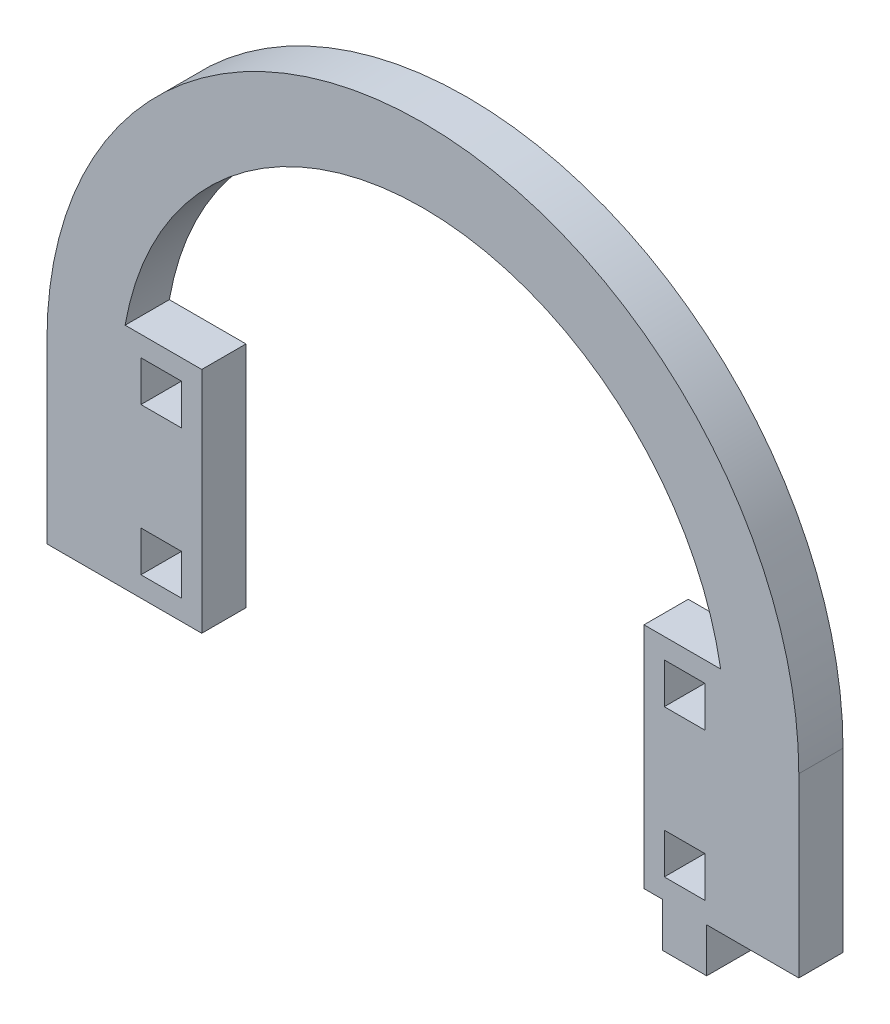
SolidWorks part; units mm, degrees
ref_plane "Front Plane" through (0, 0, 0) normal (0, 0, 1) x (1, 0, 0)
ref_plane "Top Plane" through (0, 0, 0) normal (0, 1, 0) x (1, 0, 0)
ref_plane "Right Plane" through (0, 0, 0) normal (1, 0, 0) x (0, 0, -1)
sketch "Model" plane through (0, 0, 0) normal (0, 0, 1) x (1, 0, 0)
  line L0 (3452.9004, 1295.0685) -> (3452.9004, 1271.0685)
  line L1 (3554.9004, 1295.0685) -> (3554.9004, 1271.0685)
  line L2 (3452.9004, 1271.0685) -> (3462.9004, 1271.0685)
  line L4 (3542.1504, 1279.3185) -> (3536.6504, 1279.3185)
  line L5 (3536.6504, 1279.3185) -> (3536.6504, 1273.8185)
  line L6 (3536.6504, 1273.8185) -> (3542.1504, 1273.8185)
  line L7 (3542.1504, 1273.8185) -> (3542.1504, 1279.3185)
  line L8 (3533.9004, 1271.0685) -> (3536.4004, 1271.0685)
  line L9 (3536.4004, 1271.0685) -> (3536.4004, 1265.0685)
  line L10 (3536.4004, 1265.0685) -> (3542.4004, 1265.0685)
  line L11 (3542.4004, 1265.0685) -> (3542.4004, 1271.0685)
  line L12 (3542.1504, 1299.3185) -> (3536.6504, 1299.3185)
  line L13 (3536.6504, 1299.3185) -> (3536.6504, 1293.8185)
  line L14 (3536.6504, 1293.8185) -> (3542.1504, 1293.8185)
  line L15 (3542.1504, 1293.8185) -> (3542.1504, 1299.3185)
  line L16 (3544.2984, 1302.0685) -> (3533.9004, 1302.0685)
  line L17 (3471.1504, 1279.3185) -> (3465.6504, 1279.3185)
  line L18 (3465.6504, 1279.3185) -> (3465.6504, 1273.8185)
  line L19 (3465.6504, 1273.8185) -> (3471.1504, 1273.8185)
  line L20 (3471.1504, 1273.8185) -> (3471.1504, 1279.3185)
  line L21 (3462.9004, 1271.0685) -> (3473.9004, 1271.0685)
  line L22 (3471.1504, 1299.3185) -> (3465.6504, 1299.3185)
  line L23 (3465.6504, 1299.3185) -> (3465.6504, 1293.8185)
  line L24 (3465.6504, 1293.8185) -> (3471.1504, 1293.8185)
  line L25 (3471.1504, 1293.8185) -> (3471.1504, 1299.3185)
  line L26 (3473.9004, 1302.0685) -> (3463.5024, 1302.0685)
  line L27 (3473.9004, 1302.0685) -> (3473.9004, 1271.0685)
  line L28 (3533.9004, 1302.0685) -> (3533.9004, 1271.0685)
  line L29 (3542.4004, 1271.0685) -> (3554.9004, 1271.0685)
  arc A0 (3554.9004, 1295.0685) -> (3452.9004, 1295.0685) centre (3503.9004, 1295.0685) ccw
  arc A1 (3544.2984, 1302.0685) -> (3463.5024, 1302.0685) centre (3503.9004, 1295.0685) ccw
extrude "Boss-Extrude1" add sketch "Model" along normal blind 6 contours L24 L25 L22 L23 | L19 L20 L17 L18 | L14 L15 L12 L13 | L6 L7 L4 L5 | L0 L2 L21 L27 L26 A1 L16 L28 L8 L9 L10 L11 L29 L1 A0
